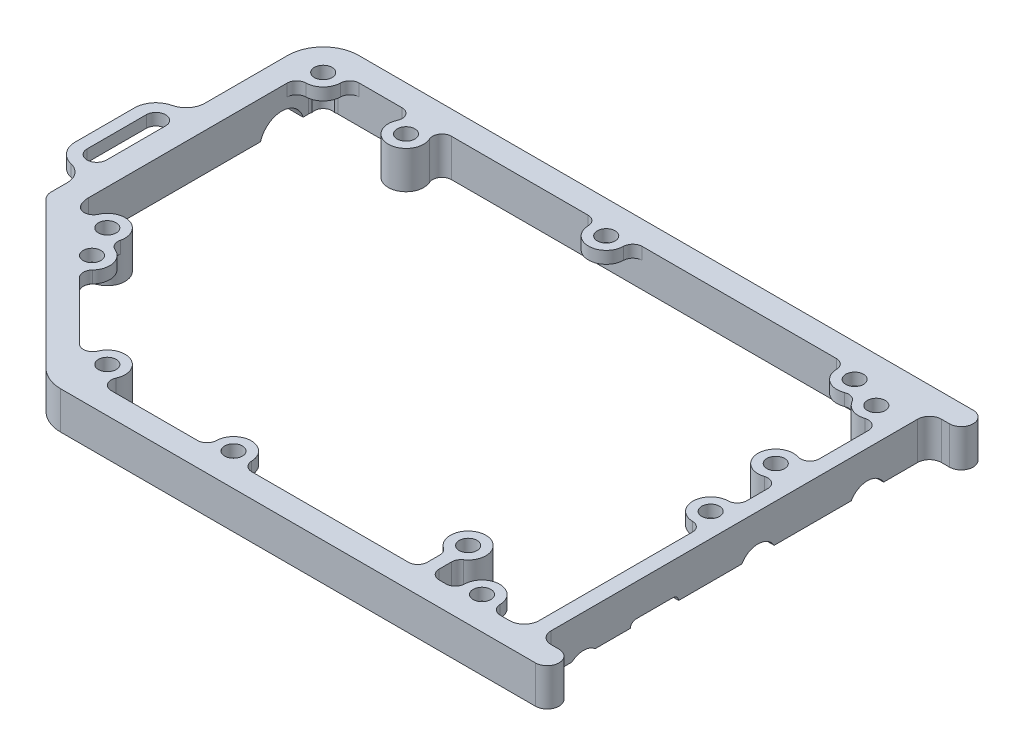
SolidWorks part; units mm, degrees
ref_plane "Front Plane" through (0, 0, 0) normal (0, 0, 1) x (1, 0, 0)
ref_plane "Top Plane" through (0, 0, 0) normal (0, 1, 0) x (1, 0, 0)
ref_plane "Right Plane" through (0, 0, 0) normal (1, 0, 0) x (0, 0, -1)
sketch "Sketch1" plane through (0, 0, 0) normal (0, 1, 0) x (1, 0, 0)
  line L25 (2.5, 5.029) -> (0, 5.029)
  line L26 (-104.3211, 17.3003) -> (-120.818, 0.8033)
  line L27 (-120.818, 0.8033) -> (-118.6967, -1.318)
  line L28 (-118.6967, -1.318) -> (-102.1997, 15.1789)
  line L29 (-96.5429, 15.1789) -> (-78.6213, -2.7426)
  line L30 (-74.3787, -4.5) -> (5.87, -4.5)
  line L31 (5.87, -0.5) -> (4.5, -0.5)
  line L32 (2.5, 1.5) -> (2.5, 5.029)
  line L34 (0, 5.029) -> (0, 2)
  line L35 (-2.5, -0.5) -> (-74.1716, -0.5)
  line L36 (-75.9393, 0.2322) -> (-98.9142, 23.2071)
  line L37 (-100, 25.8284) -> (-100, 54.9)
  line L48 (-103.377, 22.013) -> (-78.6213, -2.7426)
  line L49 (-74.3787, -4.5) -> (5.87, -4.5)
  line L50 (5.87, -0.5) -> (4.5, -0.5)
  line L54 (-2.5, -0.5) -> (-74.1716, -0.5)
  line L55 (-75.9393, 0.2322) -> (-98.9142, 23.2071)
  line L56 (-100, 25.8284) -> (-100, 63)
  line L77 (-104, 62.1) -> (-100, 62.1)
  line L78 (-100, 62.1) -> (-100, 63)
  line L79 (-97.5, 65.5) -> (-2.5, 65.5)
  line L80 (0, 63) -> (0, 57.7395)
  line L81 (0, 57.7395) -> (2.5, 57.7395)
  line L82 (2.5, 57.7395) -> (2.5, 63.5)
  line L83 (-100, 54.9) -> (-104, 54.9)
  line L85 (-104, 54.9) -> (-104, 23.5171)
  line L86 (-104, 63.5) -> (-104, 23.5171)
  line L87 (4.5, 65.5) -> (5.87, 65.5)
  line L88 (5.87, 69.5) -> (-98, 69.5)
  line L89 (-104, 63.5) -> (-104, 62.1)
  line L92 (-97.5, 65.5) -> (-2.5, 65.5)
  line L93 (0, 63) -> (0, 2)
  line L95 (2.5, 1.5) -> (2.5, 63.5)
  line L96 (4.5, 65.5) -> (5.87, 65.5)
  line L97 (5.87, 69.5) -> (-98, 69.5)
  arc A0 (-104, 23.5171) -> (-103.377, 22.013) centre (-101.8729, 23.5171) ccw
  arc A16 (-104, 23.5171) -> (-103.6236, 22.0177) centre (-100.825, 23.5171) ccw
  arc A17 (-104.3211, 17.3003) -> (-103.6236, 22.0177) centre (-107.1495, 20.1287) ccw
  arc A18 (-96.5429, 15.1789) -> (-102.1997, 15.1789) centre (-99.3713, 12.3505) ccw
  arc A19 (-78.6213, -2.7426) -> (-74.3787, -4.5) centre (-74.3787, 1.5) ccw
  arc A20 (5.87, -4.5) -> (7.87, -2.5) centre (5.87, -2.5) ccw
  arc A21 (7.87, -2.5) -> (5.87, -0.5) centre (5.87, -2.5) ccw
  arc A22 (2.5, 1.5) -> (4.5, -0.5) centre (4.5, 1.5) ccw
  arc A23 (-2.5, -0.5) -> (0, 2) centre (-2.5, 2) ccw
  arc A24 (-75.9393, 0.2322) -> (-74.1716, -0.5) centre (-74.1716, 2) ccw
  arc A25 (-100, 25.8284) -> (-98.9142, 23.2071) centre (-96.2929, 25.8284) ccw
  arc A35 (-78.6213, -2.7426) -> (-74.3787, -4.5) centre (-74.3787, 1.5) ccw
  arc A36 (5.87, -4.5) -> (7.87, -2.5) centre (5.87, -2.5) ccw
  arc A37 (7.87, -2.5) -> (5.87, -0.5) centre (5.87, -2.5) ccw
  arc A38 (2.5, 1.5) -> (4.5, -0.5) centre (4.5, 1.5) ccw
  arc A39 (-2.5, -0.5) -> (0, 2) centre (-2.5, 2) ccw
  arc A40 (-75.9393, 0.2322) -> (-74.1716, -0.5) centre (-74.1716, 2) ccw
  arc A41 (-100, 25.8284) -> (-98.9142, 23.2071) centre (-96.2929, 25.8284) ccw
  arc A68 (-97.5, 65.5) -> (-100, 63) centre (-97.5, 63) ccw
  arc A69 (0, 63) -> (-2.5, 65.5) centre (-2.5, 63) ccw
  arc A70 (4.5, 65.5) -> (2.5, 63.5) centre (4.5, 63.5) ccw
  arc A71 (5.87, 65.5) -> (7.87, 67.5) centre (5.87, 67.5) ccw
  arc A72 (7.87, 67.5) -> (5.87, 69.5) centre (5.87, 67.5) ccw
  arc A73 (-98, 69.5) -> (-104, 63.5) centre (-98, 63.5) ccw
  arc A74 (-97.5, 65.5) -> (-100, 63) centre (-97.5, 63) ccw
  arc A75 (0, 63) -> (-2.5, 65.5) centre (-2.5, 63) ccw
  arc A76 (4.5, 65.5) -> (2.5, 63.5) centre (4.5, 63.5) ccw
  arc A77 (5.87, 65.5) -> (7.87, 67.5) centre (5.87, 67.5) ccw
  arc A78 (7.87, 67.5) -> (5.87, 69.5) centre (5.87, 67.5) ccw
  arc A79 (-98, 69.5) -> (-104, 63.5) centre (-98, 63.5) ccw
  dimension "D1" = 0
  dimension "D2" = 0
extrude "Boss-Extrude1" add sketch "Sketch1" along normal blind 6.35
sketch "Sketch2" plane through (0, 6.35, 0) normal (0, -1, 0) x (1, 0, 0)
  line L1 (-107.275, -32.8633) -> (-107.275, -42.8633)
  line L2 (-104, -63.5) -> (-104, -23.5171) construction
  line L3 (-109.275, -32.8633) -> (-109.275, -42.8633)
  line L4 (-104, -26.2265) -> (-104, -32.8633)
  line L5 (-104, -42.8633) -> (-104, -49.5)
  line L6 (-106.5, -49.5) -> (-122.5, -49.5) construction
  arc A0 (-104, -32.8633) -> (-107.275, -32.8633) centre (-105.6375, -32.8633) ccw
  arc A1 (-104, -42.8633) -> (-107.275, -42.8633) centre (-105.6375, -42.8633) cw
  arc A2 (-104, -26.2265) -> (-106.4584, -29.3196) centre (-107.175, -26.2265) cw
  arc A3 (-106.4584, -29.3196) -> (-109.275, -32.8633) centre (-105.6375, -32.8633) ccw
  arc A4 (-104, -49.5) -> (-106.4584, -46.4069) centre (-107.175, -49.5) ccw
  arc A5 (-106.4584, -46.4069) -> (-109.275, -42.8633) centre (-105.6375, -42.8633) cw
  arc A6 (-104, -30.2502) -> (-104.9299, -28.0051) centre (-107.175, -30.2502) ccw construction
  dimension "D1" = 3.275
  dimension "D2" = 10
  dimension "D4" = 2
extrude "Boss-Extrude2" add sketch "Sketch2" along normal blind 2
sketch "Sketch3" plane through (0, 6.35, 0) normal (0, 1, 0) x (1, 0, 0)
  line L0 (-86.6698, 65.5) -> (-78.3302, 65.5)
  line L1 (-99.6046, 24.1625) -> (-99.1422, 20.8407)
  line L2 (-99.1422, 20.8407) -> (-93.3524, 17.6453)
  line L3 (-79.3547, 3.6476) -> (-74.7525, -2.0465)
  line L4 (-74.7525, -2.0465) -> (-69.8302, -0.5)
  line L5 (0, 49.3646) -> (0, 40.6354)
  line L6 (-7.1698, 65.5) -> (1.1439, 66.6572)
  line L7 (1.1439, 66.6572) -> (0, 57.6354)
  arc A0 (-99.6046, 24.1625) -> (-96.7377, 24.2268) centre (-98.1864, 24.8759) ccw construction
  arc A1 (-92.8424, 20.2323) -> (-96.7377, 24.2268) centre (-94, 23) ccw construction
  arc A2 (-92.8424, 20.2323) -> (-93.3524, 17.6453) centre (-92.2298, 18.7678) ccw construction
  arc A3 (-79.3547, 3.6476) -> (-76.7677, 4.1576) centre (-78.2322, 4.7702) ccw construction
  arc A4 (-71.2731, 1.7493) -> (-76.7677, 4.1576) centre (-74, 3) ccw construction
  arc A5 (-71.2731, 1.7493) -> (-69.8302, -0.5) centre (-69.8302, 1.0875) ccw construction
  circle A6 centre (-17, 7) radius 3 construction
  arc A7 (0, 40.6354) -> (-2.0763, 42.1457) centre (-1.5875, 40.6354) ccw construction
  arc A8 (-4.6, 42.4623) -> (-2.0763, 42.1457) centre (-3, 45) ccw construction
  arc A9 (-4.6, 47.5377) -> (-4.6, 42.4623) centre (-3, 45) ccw construction
  arc A10 (-2.0763, 47.8543) -> (-4.6, 47.5377) centre (-3, 45) ccw construction
  arc A11 (-2.0763, 47.8543) -> (0, 49.3646) centre (-1.5875, 49.3646) ccw construction
  arc A19 (0, 57.6354) -> (-2.0763, 59.1457) centre (-1.5875, 57.6354) ccw construction
  arc A20 (-5.7269, 63.2507) -> (-2.0763, 59.1457) centre (-3, 62) ccw construction
  arc A21 (-5.7269, 63.2507) -> (-7.1698, 65.5) centre (-7.1698, 63.9125) ccw construction
  arc A22 (-85.2269, 63.2507) -> (-79.7731, 63.2507) centre (-82.5, 62) ccw construction
  arc A23 (-85.2269, 63.2507) -> (-86.6698, 65.5) centre (-86.6698, 63.9125) ccw construction
  arc A24 (-78.3302, 65.5) -> (-79.7731, 63.2507) centre (-78.3302, 63.9125) ccw construction
  arc A25 (-99.6046, 24.1625) -> (-96.7377, 24.2268) centre (-98.1864, 24.8759) ccw
  arc A26 (-92.8424, 20.2323) -> (-96.7377, 24.2268) centre (-94, 23) ccw
  arc A27 (-92.8424, 20.2323) -> (-93.3524, 17.6453) centre (-92.2298, 18.7678) ccw
  arc A28 (-79.3547, 3.6476) -> (-76.7677, 4.1576) centre (-78.2322, 4.7702) ccw
  arc A29 (-71.2731, 1.7493) -> (-76.7677, 4.1576) centre (-74, 3) ccw
  arc A30 (-71.2731, 1.7493) -> (-69.8302, -0.5) centre (-69.8302, 1.0875) ccw
  circle A31 centre (-17, 7) radius 3
  arc A32 (0, 40.6354) -> (-2.0763, 42.1457) centre (-1.5875, 40.6354) ccw
  arc A33 (-4.6, 42.4623) -> (-2.0763, 42.1457) centre (-3, 45) ccw
  arc A34 (-4.6, 47.5377) -> (-4.6, 42.4623) centre (-3, 45) ccw
  arc A35 (-2.0763, 47.8543) -> (-4.6, 47.5377) centre (-3, 45) ccw
  arc A36 (-2.0763, 47.8543) -> (0, 49.3646) centre (-1.5875, 49.3646) ccw
  arc A37 (0, 57.6354) -> (-2.0763, 59.1457) centre (-1.5875, 57.6354) ccw
  arc A38 (-5.7269, 63.2507) -> (-2.0763, 59.1457) centre (-3, 62) ccw
  arc A39 (-5.7269, 63.2507) -> (-7.1698, 65.5) centre (-7.1698, 63.9125) ccw
  arc A40 (-85.2269, 63.2507) -> (-79.7731, 63.2507) centre (-82.5, 62) ccw
  arc A41 (-85.2269, 63.2507) -> (-86.6698, 65.5) centre (-86.6698, 63.9125) ccw
  arc A42 (-78.3302, 65.5) -> (-79.7731, 63.2507) centre (-78.3302, 63.9125) ccw
extrude "Boss-Extrude3" add sketch "Sketch3" against normal up to surface (6.35 mm away) up to face at (-37.378, 0, -30.8604)
sketch "Sketch4" plane through (0, 6.35, 0) normal (0, 1, 0) x (1, 0, 0)
  line L0 (-17, 7) -> (-17, -0.5) construction
  line L1 (-69.8302, -0.5) -> (-2.5, -0.5) construction
  line L2 (-18, 7) -> (-16, 7)
  line L3 (-18, 7) -> (-18, -0.5)
  line L4 (-18, -0.5) -> (-16, -0.5)
  line L5 (-16, -0.5) -> (-16, 7)
  line L6 (-19.5875, -0.5) -> (-18, -0.5)
  line L7 (-16, -0.5) -> (-14.4125, -0.5)
  arc A0 (-18.6921, 4.5227) -> (-18, 3.2119) centre (-19.5875, 3.2119) cw
  circle A1 centre (-17, 7) radius 3 construction
  arc A2 (-18, 1.0875) -> (-19.5875, -0.5) centre (-19.5875, 1.0875) cw
  arc A3 (-15.3079, 4.5227) -> (-16, 3.2119) centre (-14.4125, 3.2119) ccw
  arc A4 (-16, 1.0875) -> (-14.4125, -0.5) centre (-14.4125, 1.0875) ccw
  arc A5 (-13.2435, -0.5) -> (-11.6563, 1.0572) centre (-13.2435, 1.0875) ccw construction
  circle M1 centre (-17, 7) radius 3
  dimension "D1" = 2
extrude "Boss-Extrude4" add sketch "Sketch4" against normal up to surface (6.35 mm away) contours L3 A2 L6 | A4 L5 L7 | A0 L3 M1 | A3 L5 M1 | L0 L4 L5 M1 | L0 L3 L4 M1
sketch "Sketch5" plane through (0, 6.35, 0) normal (0, 1, 0) x (1, 0, 0)
  circle A0 centre (-82.5, 62) radius 1.5
  circle A1 centre (-94, 23) radius 1.5
  circle A2 centre (-74, 3) radius 1.5
  circle A3 centre (-17, 7) radius 1.5
  circle A4 centre (-3, 45) radius 1.5
  circle A5 centre (-3, 62) radius 1.5
  dimension "D1" = 3
extrude "Cut-Extrude1" cut sketch "Sketch5" against normal through all
sketch "Sketch7" plane through (0, 6.35, 0) normal (0, 1, 0) x (1, 0, 0)
  line L0 (-55.2435, 65.5) -> (-46.0702, 65.5)
  line L1 (-5.6062, 60.5141) -> (-4.3857, 66.735)
  line L2 (-4.3857, 66.735) -> (-13.2435, 65.5)
  line L3 (0, 27.9133) -> (0, 37.0867)
  line L4 (-13.2435, -0.5) -> (-4.0702, -0.5)
  line L5 (-55.2435, -0.5) -> (-46.0702, -0.5)
  line L6 (-91.0839, 22.2955) -> (-96.1532, 18.2949)
  line L7 (-96.1532, 18.2949) -> (-89.0694, 13.3623)
  line L8 (-100, 59.4133) -> (-101.0208, 66.735)
  line L9 (-101.0208, 66.735) -> (-93.9133, 65.5)
  arc A0 (-93.9133, 65.5) -> (-95.5005, 63.9428) centre (-93.9133, 63.9125) ccw construction
  arc A1 (-98.4428, 61.0005) -> (-95.5005, 63.9428) centre (-98.5, 64) ccw construction
  arc A2 (-98.4428, 61.0005) -> (-100, 59.4133) centre (-98.4125, 59.4133) ccw construction
  arc A3 (-91.0839, 22.2955) -> (-90.133, 20.4497) centre (-89.5408, 21.9226) ccw construction
  arc A4 (-89.0907, 15.5858) -> (-90.133, 20.4497) centre (-91.252, 17.6663) ccw construction
  arc A5 (-89.0907, 15.5858) -> (-89.0694, 13.3623) centre (-87.9469, 14.4849) ccw construction
  arc A6 (-55.2435, -0.5) -> (-53.6563, 1.0572) centre (-55.2435, 1.0875) ccw construction
  arc A7 (-47.6574, 1.0572) -> (-53.6563, 1.0572) centre (-50.6569, 1) ccw construction
  arc A8 (-47.6574, 1.0572) -> (-46.0702, -0.5) centre (-46.0702, 1.0875) ccw construction
  arc A9 (-13.2435, -0.5) -> (-11.6563, 1.0572) centre (-13.2435, 1.0875) ccw construction
  arc A10 (-5.6574, 1.0572) -> (-11.6563, 1.0572) centre (-8.6569, 1) ccw construction
  arc A11 (-5.6574, 1.0572) -> (-4.0702, -0.5) centre (-4.0702, 1.0875) ccw construction
  arc A12 (0, 27.9133) -> (-1.5572, 29.5005) centre (-1.5875, 27.9133) ccw construction
  arc A13 (-1.5572, 35.4995) -> (-1.5572, 29.5005) centre (-1.5, 32.5) ccw construction
  arc A14 (-1.5572, 35.4995) -> (0, 37.0867) centre (-1.5875, 37.0867) ccw construction
  arc A15 (-5.6062, 60.5141) -> (-7.5637, 61.2062) centre (-6.9853, 59.7279) ccw construction
  arc A16 (-11.6563, 63.9428) -> (-7.5637, 61.2062) centre (-8.6569, 64) ccw construction
  arc A17 (-11.6563, 63.9428) -> (-13.2435, 65.5) centre (-13.2435, 63.9125) ccw construction
  arc A18 (-53.6563, 63.9428) -> (-55.2435, 65.5) centre (-55.2435, 63.9125) ccw construction
  arc A19 (-53.6563, 63.9428) -> (-47.6574, 63.9428) centre (-50.6569, 64) ccw construction
  arc A20 (-46.0702, 65.5) -> (-47.6574, 63.9428) centre (-46.0702, 63.9125) ccw construction
  arc A21 (-93.9133, 65.5) -> (-95.5005, 63.9428) centre (-93.9133, 63.9125) ccw
  arc A22 (-98.4428, 61.0005) -> (-95.5005, 63.9428) centre (-98.5, 64) ccw
  arc A23 (-98.4428, 61.0005) -> (-100, 59.4133) centre (-98.4125, 59.4133) ccw
  arc A24 (-91.0839, 22.2955) -> (-90.133, 20.4497) centre (-89.5408, 21.9226) ccw
  arc A25 (-89.0907, 15.5858) -> (-90.133, 20.4497) centre (-91.252, 17.6663) ccw
  arc A26 (-89.0907, 15.5858) -> (-89.0694, 13.3623) centre (-87.9469, 14.4849) ccw
  arc A27 (-55.2435, -0.5) -> (-53.6563, 1.0572) centre (-55.2435, 1.0875) ccw
  arc A28 (-47.6574, 1.0572) -> (-53.6563, 1.0572) centre (-50.6569, 1) ccw
  arc A29 (-47.6574, 1.0572) -> (-46.0702, -0.5) centre (-46.0702, 1.0875) ccw
  arc A30 (-13.2435, -0.5) -> (-11.6563, 1.0572) centre (-13.2435, 1.0875) ccw
  arc A31 (-5.6574, 1.0572) -> (-11.6563, 1.0572) centre (-8.6569, 1) ccw
  arc A32 (-5.6574, 1.0572) -> (-4.0702, -0.5) centre (-4.0702, 1.0875) ccw
  arc A33 (0, 27.9133) -> (-1.5572, 29.5005) centre (-1.5875, 27.9133) ccw
  arc A34 (-1.5572, 35.4995) -> (-1.5572, 29.5005) centre (-1.5, 32.5) ccw
  arc A35 (-1.5572, 35.4995) -> (0, 37.0867) centre (-1.5875, 37.0867) ccw
  arc A36 (-5.6062, 60.5141) -> (-7.5637, 61.2062) centre (-6.9853, 59.7279) ccw
  arc A37 (-11.6563, 63.9428) -> (-7.5637, 61.2062) centre (-8.6569, 64) ccw
  arc A38 (-11.6563, 63.9428) -> (-13.2435, 65.5) centre (-13.2435, 63.9125) ccw
  arc A39 (-53.6563, 63.9428) -> (-55.2435, 65.5) centre (-55.2435, 63.9125) ccw
  arc A40 (-53.6563, 63.9428) -> (-47.6574, 63.9428) centre (-50.6569, 64) ccw
  arc A41 (-46.0702, 65.5) -> (-47.6574, 63.9428) centre (-46.0702, 63.9125) ccw
extrude "Boss-Extrude5" add sketch "Sketch7" against normal offset from surface (2.05 mm away) 0.5
sketch "Sketch8" plane through (0, 6.35, 0) normal (0, 1, 0) x (1, 0, 0)
  circle A0 centre (-98.5, 64) radius 1.5
  circle A1 centre (-50.6569, 64) radius 1.5
  circle A2 centre (-91.252, 17.6663) radius 1.5
  circle A3 centre (-50.6569, 1) radius 1.5
  circle A4 centre (-8.6569, 1) radius 1.5
  circle A5 centre (-1.5, 32.5) radius 1.5
  circle A6 centre (-8.6569, 64) radius 1.5
  dimension "D1" = 3
extrude "Cut-Extrude2" cut sketch "Sketch8" against normal through all
sketch "Sketch9" plane through (2.5, 0, 0) normal (1, 0, 0) x (0, 0, -1)
  line L4 (15.2, -2.43) -> (22.8, -2.43)
  line L5 (23.1, -2.13) -> (23.1, -0.1)
  line L6 (22.1, 0.9) -> (15.9, 0.9)
  line L7 (14.9, -0.1) -> (14.9, -2.13)
  line L8 (15.2, -2.43) -> (22.8, -2.43)
  line L9 (23.1, -2.13) -> (23.1, -0.1)
  line L10 (22.1, 0.9) -> (15.9, 0.9)
  line L11 (14.9, -0.1) -> (14.9, -2.13)
  circle A0 centre (6.9997, -2.26) radius 2.9985
  circle A1 centre (36.5, -1.605) radius 3.175
  circle A2 centre (55, -1.605) radius 3.175
  arc A7 (22.8, -2.43) -> (23.1, -2.13) centre (22.8, -2.13) ccw
  arc A8 (23.1, -0.1) -> (22.1, 0.9) centre (22.1, -0.1) ccw
  arc A9 (15.9, 0.9) -> (14.9, -0.1) centre (15.9, -0.1) ccw
  arc A10 (14.9, -2.13) -> (15.2, -2.43) centre (15.2, -2.13) ccw
  arc A11 (22.8, -2.43) -> (23.1, -2.13) centre (22.8, -2.13) ccw
  arc A12 (23.1, -0.1) -> (22.1, 0.9) centre (22.1, -0.1) ccw
  arc A13 (15.9, 0.9) -> (14.9, -0.1) centre (15.9, -0.1) ccw
  arc A14 (14.9, -2.13) -> (15.2, -2.43) centre (15.2, -2.13) ccw
  dimension "D1" = 0
extrude "Cut-Extrude3" cut sketch "Sketch9" against normal blind 12.5
sketch "Sketch10" plane through (-104, 0, 0) normal (-1, 0, 0) x (0, 0, 1)
  circle A0 centre (-58.5, -1.05) radius 3.75
extrude "Cut-Extrude4" cut sketch "Sketch10" against normal blind 12.5
